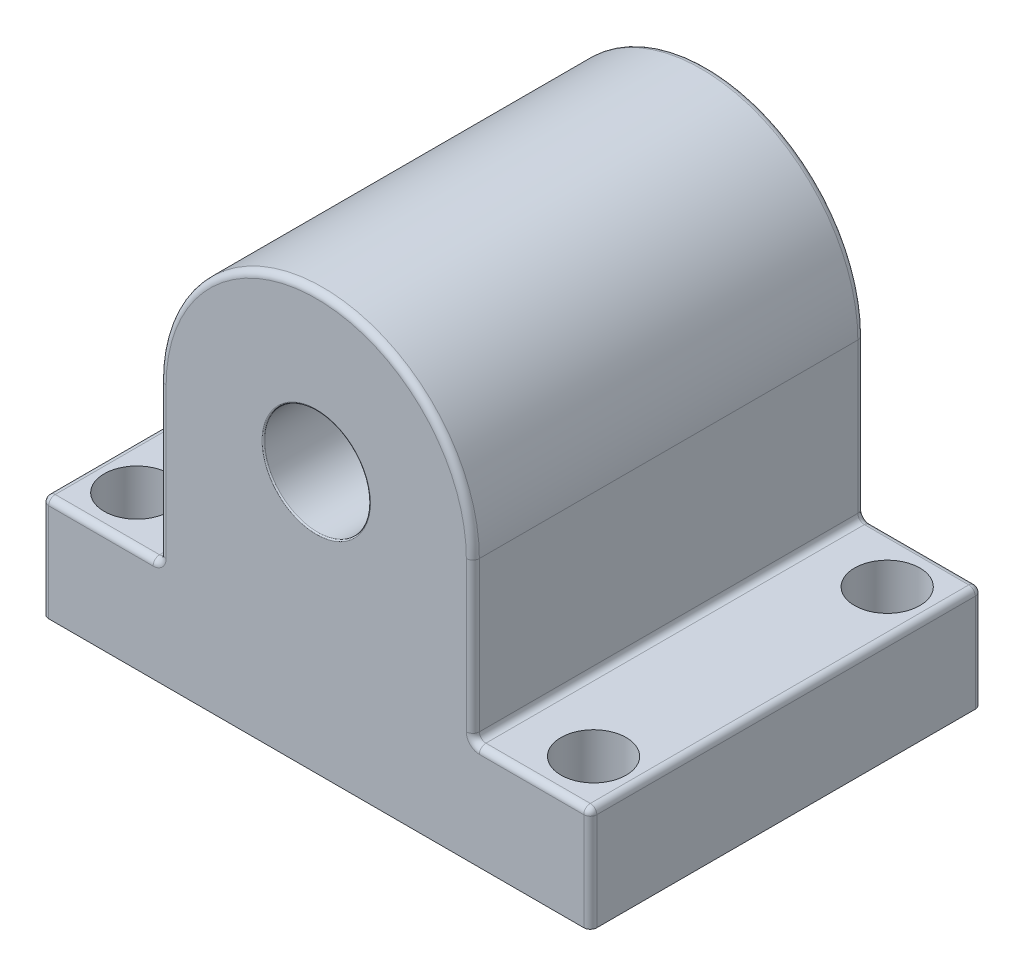
SolidWorks part; units mm, degrees
material "PBT General Purpose"
ref_plane "Front Plane" through (0, 0, 0) normal (0, 0, 1) x (1, 0, 0)
ref_plane "Top Plane" through (0, 0, 0) normal (0, 1, 0) x (1, 0, 0)
ref_plane "Right Plane" through (0, 0, 0) normal (1, 0, 0) x (0, 0, -1)
sketch "Croquis1" plane through (0, 0, 0) normal (0, 0, 1) x (1, 0, 0)
  line L0 (21, 0) -> (-21, 0)
  line L1 (-21, 0) -> (-21, 20) construction
  line L3 (21, 20) -> (21, 0) construction
  line L4 (4.05, 20) -> (-4.05, 20) construction
  line L5 (-4.05, 20) -> (-21, 20) construction
  line L6 (4.05, 20) -> (21, 20) construction
  line L7 (0, 20) -> (0, 0) construction
  line L8 (-21, 0) -> (-21, 8)
  line L9 (-21, 8) -> (-12, 8)
  line L10 (-12, 8) -> (-12, 20)
  line L11 (12, 20) -> (12, 8)
  line L12 (12, 8) -> (21, 8)
  line L13 (21, 8) -> (21, 0)
  line L14 (12, 8) -> (-12, 8) construction
  circle A0 centre (0, 20) radius 4.05
  arc A1 (12, 20) -> (-12, 20) centre (0, 20) ccw
  point P4 (0, 0)
  point P13 (0, 20)
  dimension "D1" = 8.1
  dimension "D2" = 12
  dimension "D3" = 20
  dimension "D4" = 42
  dimension "D5" = 8
extrude "Saliente-Extruir1" add sketch "Croquis1" against normal mid plane 30 contours A0 L5 L1 L0 L3 L6 | L6 A1 L5 A0
sketch "Croquis2" plane through (0, 8, 0) normal (0, 1, 0) x (1, 0, 0)
  line L1 (17.5, -11.25) -> (-17.5, -11.25) construction
  line L2 (17.5, -11.25) -> (17.5, 11.25) construction
  line L3 (17.5, 11.25) -> (-17.5, 11.25) construction
  line L4 (-17.5, -11.25) -> (-17.5, 11.25) construction
  line L5 (17.5, -11.25) -> (-17.5, 11.25) construction
  line L6 (17.5, 11.25) -> (-17.5, -11.25) construction
  circle A0 centre (-17.5, 11.25) radius 2.5
  circle A1 centre (17.5, 11.25) radius 2.5
  circle A2 centre (-17.5, -11.25) radius 2.5
  circle A3 centre (17.5, -11.25) radius 2.5
  point P0 (0, 0)
  dimension "D3" = 5
  dimension "D1" = 35
  dimension "D2" = 22.5
extrude "Cortar-Extruir1" cut sketch "Croquis2" against normal up to next
fillet "Redondeo1" radius 0.5 18 edges at (16.5, 8, 15) (16.5, 8, -15) (12, 14, 15) (12, 14, -15) (0, 32, 15) (0, 32, -15) (-16.5, 8, -15) (-12, 14, 15) (-12, 14, -15) (-21, 4, -15) (21, 4, -15) (21, 4, 15) (-21, 4, 15) (21, 8, 0) (12, 8, 0) (-21, 8, 0) (-16.5, 8, 15) (-12, 8, 0)
fillet "Redondeo2" radius 0.1 2 edges at (4.05, 20, -15) (4.05, 20, 15)
